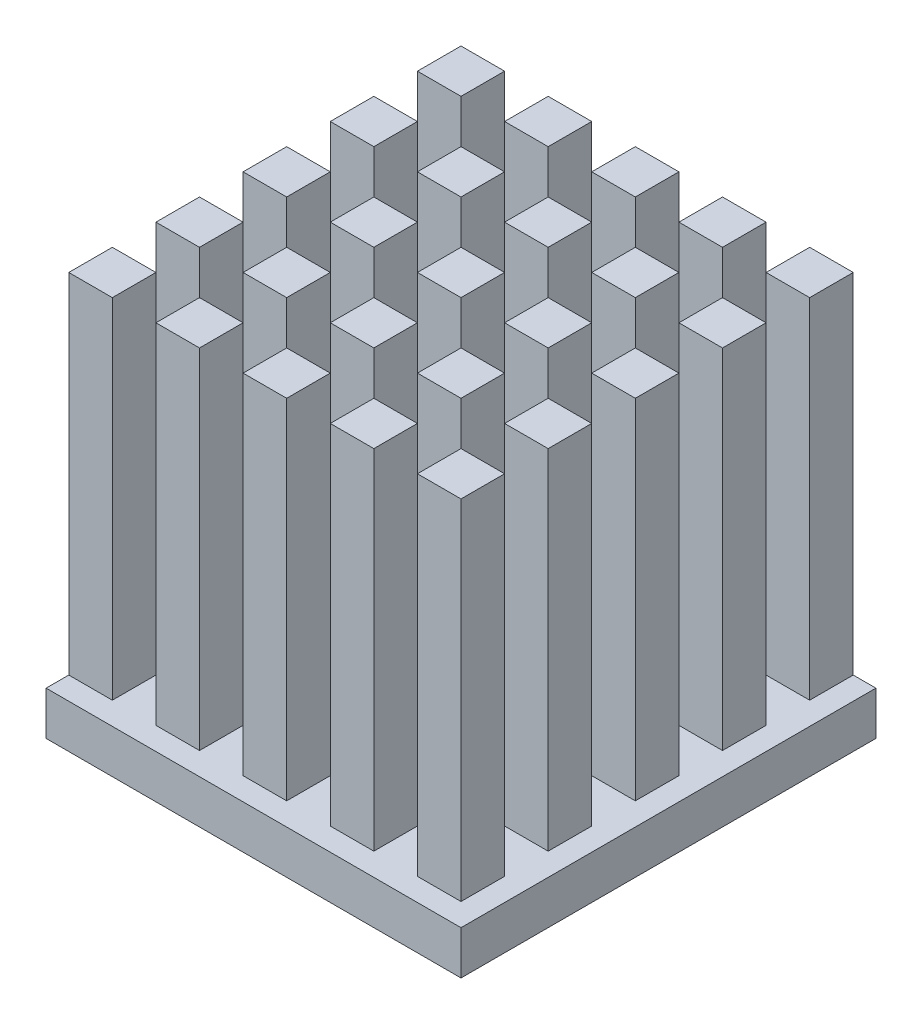
SolidWorks part; units mm, degrees
material "Copper"
ref_plane "Front Plane" through (0, 0, 0) normal (0, 0, 1) x (1, 0, 0)
ref_plane "Top Plane" through (0, 0, 0) normal (0, 1, 0) x (1, 0, 0)
ref_plane "Right Plane" through (0, 0, 0) normal (1, 0, 0) x (0, 0, -1)
sketch "Sketch1" plane through (0, 0, 0) normal (0, 1, 0) x (1, 0, 0)
  line L1 (-7.14, 7.14) -> (7.14, 7.14)
  line L2 (-7.14, 7.14) -> (-7.14, -7.14)
  line L3 (-7.14, -7.14) -> (7.14, -7.14)
  line L4 (7.14, 7.14) -> (7.14, -7.14)
  line L5 (-7.14, 7.14) -> (7.14, -7.14) construction
  line L6 (-7.14, -7.14) -> (7.14, 7.14) construction
  point P0 (0, 0)
  dimension "D1" = 14.28
extrude "Boss-Extrude1" add sketch "Sketch1" along normal blind 1.5
sketch "Sketch3" plane through (0, 1.5, 0) normal (0, 1, 0) x (1, 0, 0)
  line L1 (-7.14, 7.14) -> (-5.64, 7.14)
  line L2 (-7.14, 7.14) -> (-7.14, 5.64)
  line L3 (-7.14, 5.64) -> (-5.64, 5.64)
  line L4 (-5.64, 7.14) -> (-5.64, 5.64)
  dimension "D1" = 1.5
extrude "Boss-Extrude3" add sketch "Sketch3" along normal blind 12
pattern_linear "LPattern2" count 5 spacing 3 along (1, 0, 0) count 5 spacing 3 along (0, 0, 1) of "Boss-Extrude3"
